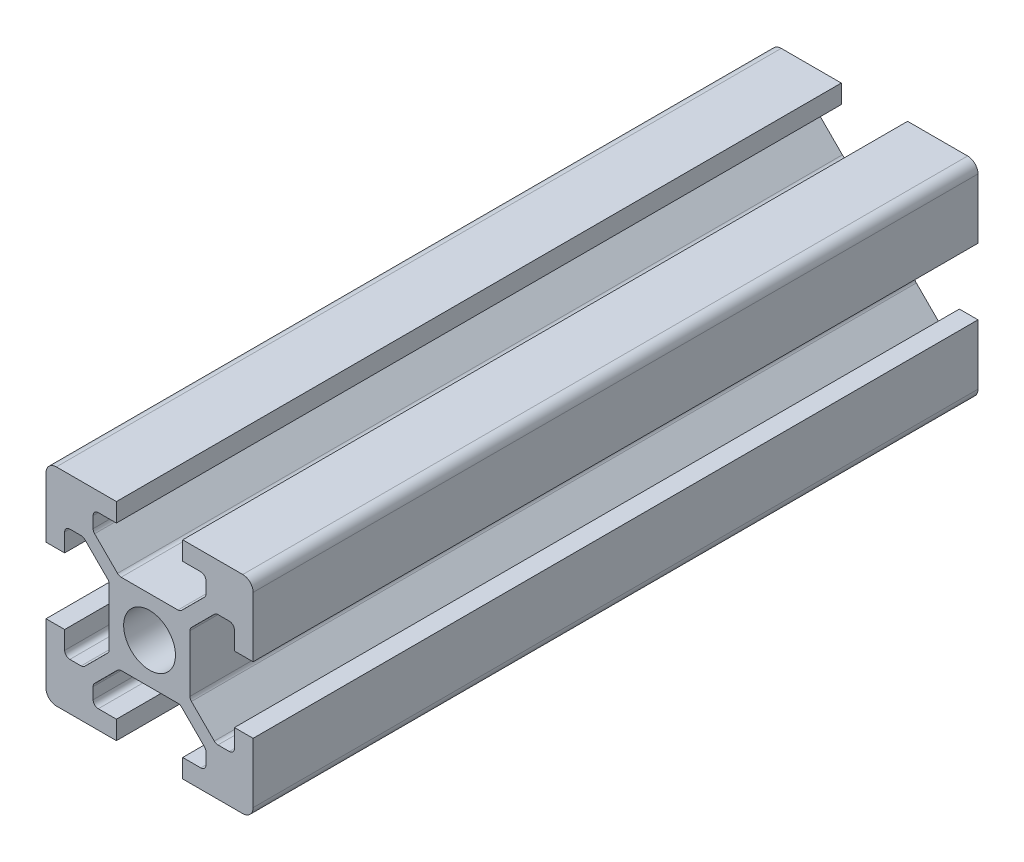
SolidWorks part; units mm, degrees
material "1060 Alloy"
ref_plane "Front Plane" through (0, 0, 0) normal (0, 0, 1) x (1, 0, 0)
ref_plane "Top Plane" through (0, 0, 0) normal (0, 1, 0) x (1, 0, 0)
ref_plane "Right Plane" through (0, 0, 0) normal (1, 0, 0) x (0, 0, -1)
sketch "Sketch1" plane through (0, 0, 0) normal (0, 0, 1) x (1, 0, 0)
  line L0 (20, 0) -> (-8.059, 28.059) construction
  line L1 (0, 0) -> (6.8, 0)
  line L2 (0, 0) -> (0, 6.8)
  line L3 (0, 20) -> (6.8, 20)
  line L4 (20, 0) -> (20, 6.8)
  line L5 (6.8, 20) -> (6.8, 18.2)
  line L6 (20, 20) -> (8.2322, 8.2322) construction
  line L7 (12.95, 6.1) -> (7.05, 6.1)
  line L8 (13.9, 7.05) -> (13.9, 12.95)
  line L9 (12.95, 13.9) -> (7.05, 13.9)
  line L10 (6.1, 7.05) -> (6.1, 12.95)
  line L11 (13.9, 6.1) -> (6.1, 13.9) construction
  line L12 (13.9, 13.9) -> (6.1, 6.1) construction
  line L13 (4.55, 16.4) -> (7.05, 13.9)
  line L14 (13.2, 18.2) -> (13.2, 20)
  line L15 (1.8, 6.8) -> (0, 6.8)
  line L16 (0, 13.2) -> (0, 20)
  line L17 (0, 13.2) -> (1.8, 13.2)
  line L18 (10, 10) -> (10, 13.9) construction
  line L19 (16.4, 4.55) -> (13.9, 7.05)
  line L20 (4.55, 16.4) -> (4.55, 18.2)
  line L21 (4.55, 18.2) -> (6.8, 18.2)
  line L22 (13.2, 18.2) -> (15.45, 18.2)
  line L23 (15.45, 18.2) -> (15.45, 16.4)
  line L24 (15.45, 16.4) -> (12.95, 13.9)
  line L25 (16.4, 4.55) -> (18.2, 4.55)
  line L26 (18.2, 4.55) -> (18.2, 6.8)
  line L27 (20, 6.8) -> (18.2, 6.8)
  line L28 (18.2, 13.2) -> (20, 13.2)
  line L29 (18.2, 13.2) -> (18.2, 15.45)
  line L30 (18.2, 15.45) -> (16.4, 15.45)
  line L31 (16.4, 15.45) -> (13.9, 12.95)
  line L32 (1.8, 4.55) -> (3.6, 4.55)
  line L33 (3.6, 15.45) -> (6.1, 12.95)
  line L34 (3.6, 15.45) -> (1.8, 15.45)
  line L35 (1.8, 15.45) -> (1.8, 13.2)
  line L36 (0, 13.2) -> (1.8, 13.2)
  line L37 (1.8, 6.8) -> (0, 6.8)
  line L38 (3.6, 4.55) -> (6.1, 7.05)
  line L39 (1.8, 6.8) -> (1.8, 4.55)
  line L40 (15.45, 3.6) -> (12.95, 6.1)
  line L41 (4.55, 3.6) -> (7.05, 6.1)
  line L42 (4.55, 1.8) -> (4.55, 3.6)
  line L43 (6.8, 1.8) -> (4.55, 1.8)
  line L44 (6.8, 1.8) -> (6.8, 0)
  line L45 (15.45, 3.6) -> (15.45, 1.8)
  line L46 (15.45, 1.8) -> (13.2, 1.8)
  line L47 (13.2, 0) -> (13.2, 1.8)
  line L48 (13.2, 20) -> (20, 20)
  line L49 (20, 13.2) -> (20, 20)
  line L50 (13.2, 0) -> (20, 0)
  line L51 (6.1, 6.1) -> (-5.5045, -5.5045) construction
  circle A0 centre (10, 10) radius 2.5
  point P25 (10, 16.4)
  point P39 (13.2, 19.1)
  point P46 (0.9, 6.8)
  dimension "D3" = 5
  dimension "D2" = 20
  dimension "D4" = 7.8
  dimension "D5" = 7.8
  dimension "D6" = 6.8
  dimension "D7" = 6.8
  dimension "D8" = 1.8
  dimension "D9" = 10.9
  dimension "D10" = 1.8
  dimension "D11" = 10.9
  dimension "D12" = 20
extrude "Boss-Extrude1" add sketch "Sketch1" along normal blind 70 contours L47 L50 L4 L27 L26 L25 L19 L8 L31 L30 L29 L28 L49 L48 L14 L22 L23 L24 L9 L13 L20 L21 L5 L3 L16 L17 L35 L34 L33 L10 L38 L32 L39 L15 L2 L1 L44 L43 L42 L41 L7 L40 L45 L46 A0
fillet "Fillet1" radius 1 4 edges at (20, 20, 35) (20, 0, 35) (0, 0, 35) (0, 20, 35)
fillet "Fillet2" radius 0.5 6 edges at (4.55, 18.2, 35) (4.55, 16.4, 35) (7.05, 13.9, 35) (15.45, 18.2, 35) (15.45, 16.4, 35) (12.95, 13.9, 35)
fillet "Fillet3" radius 0.5 6 edges at (18.2, 15.45, 35) (16.4, 15.45, 35) (13.9, 12.95, 35) (18.2, 4.55, 35) (13.9, 7.05, 35) (16.4, 4.55, 35)
fillet "Fillet4" radius 0.5 6 edges at (1.8, 15.45, 35) (3.6, 15.45, 35) (6.1, 12.95, 35) (3.6, 4.55, 35) (1.8, 4.55, 35) (6.1, 7.05, 35)
fillet "Fillet5" radius 0.5 6 edges at (7.05, 6.1, 35) (4.55, 3.6, 35) (4.55, 1.8, 35) (15.45, 1.8, 35) (15.45, 3.6, 35) (12.95, 6.1, 35)
